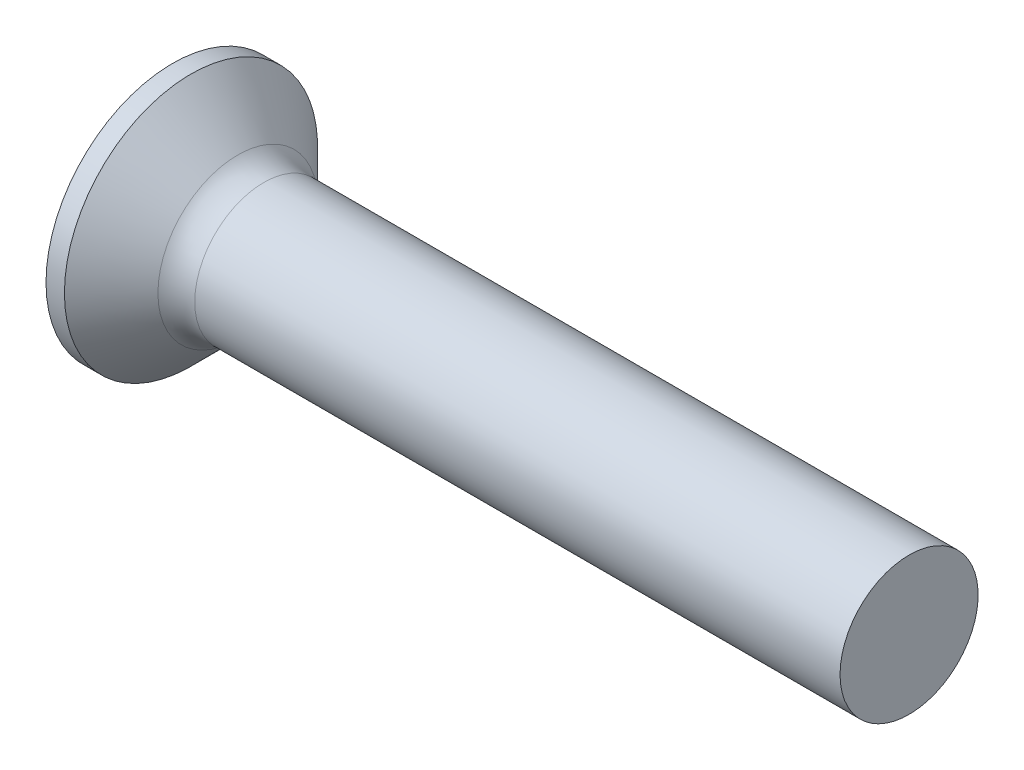
SolidWorks part; units mm, degrees
revolve "Base-Revolve" add sketch "BodySke"
sketch "BodySke" plane through (0, 0, 0) normal (0, 0, 1) x (1, 0, 0)
  line L0 (0, 0) -> (0, 2.75)
  line L1 (0, 2.75) -> (0.4, 2.75)
  line L2 (1.65, 1.5) -> (16, 1.5)
  line L3 (16, 1.5) -> (16, 0)
  line L4 (16, 0) -> (0, 0)
  line L5 (-6.35, 0) -> (82.55, 0) construction
  line L6 (1.65, -1.5) -> (16, -1.5) construction
  line L7 (0.4, -2.75) -> (1.65, -1.5) construction
  line L8 (0.4, 2.75) -> (1.65, 1.5)
  line L9 (0, -2.75) -> (0.4, -2.75) construction
  line L10 (2.15, 3.0875) -> (2.15, -6.4375) construction
  line L11 (0, 6.35) -> (0, -3.175) construction
  dimension "Diameter" = 3
  dimension "Length" = 16
  dimension "Head_ht" = 1.65
  dimension "Head_dia" = 5.5
  dimension "Head_ang" = 90
  dimension "D6" = 0.4
  dimension "Advance" = 0.5
  dimension "Thread_nom" = 16
cosmetic thread "ThreadCosmetic" [suppressed]
fillet "Fillet1" radius 0.8 1 edges at (1.65, 0, 1.5)
ref_plane "Plane1" through (0, 0, 0) normal (0, 0, 1) x (1, 0, 0)
ref_plane "Plane2" through (0, 0, 0) normal (0, 1, 0) x (1, 0, 0)
ref_plane "Plane3" through (0, 0, 0) normal (1, 0, 0) x (0, 0, -1)
sketch "Sketch3" plane through (0, 0, 0) normal (-1, 0, 0) x (0, 0, 1)
  line L0 (-0.37, 1.5) -> (0.37, 1.5)
  line L1 (0.37, 1.5) -> (0.37, -1.5)
  line L2 (0.37, -1.5) -> (-0.37, -1.5)
  line L3 (-0.37, -1.5) -> (-0.37, 1.5)
  dimension "Cross_dia" = 3
  dimension "Cross_width" = 0.74
  dimension "D1" = 1.5
  dimension "D2" = 0.37
ref_plane "Plane4" through (2.01, 0, 0) normal (-1, 0, 0) x (0, 0, 1)
sketch "Sketch4" plane through (2.01, 0, 0) normal (-1, 0, 0) x (0, 0, 1)
  line L0 (-0.37, 0.4979) -> (0.37, 0.4979)
  line L3 (0.37, 0.4979) -> (0.37, -0.4979)
  line L4 (0.37, -0.4979) -> (-0.37, -0.4979)
  line L5 (-0.37, -0.4979) -> (-0.37, 0.4979)
  dimension "D2" = 0.9957
  dimension "D1" = 0.74
  dimension "D4" = 0.4979
  dimension "D3" = 0.37
loft "Recess" cut profiles "Sketch3", "Sketch4"
pattern_circular "RecPat" count 2 every 90 about axis through (0, 0, 0) along (1, 0, 0) of "Recess"
sketch "RecCorSke" plane through (0, 0, 0) normal (0, 0, 1) x (1, 0, 0)
  line L0 (-3.175, 0) -> (15.875, 0) construction
  line L2 (0, 0) -> (0, 0.6966)
  line L3 (0, 0.6966) -> (2.01, 0.556)
  line L4 (2.01, 0.556) -> (2.1907, 0)
  line L5 (2.1907, 0) -> (0, 0)
  dimension "Diameter" = 1.112
  dimension "Depth" = 2.01
  dimension "Draft_angle" = 4
  dimension "Bottom_angle" = 18
revolve "RecessCore" cut sketch "RecCorSke" angle 360 about L0
sketch "ThdSchSke" plane through (0, 0, 0) normal (0, 0, 1) x (1, 0, 0)
  line L0 (2.15, -1.2195) -> (1.9536, -1.5)
  line L1 (2.15, -1.2195) -> (2.3464, -1.5)
  line L2 (2.3464, -1.5) -> (2.3464, -1.875)
  line L3 (-3.175, 0) -> (5.1513, 0) construction
  line L5 (2.3464, -1.875) -> (1.9536, -1.875)
  line L6 (1.9536, -1.875) -> (1.9536, -1.5)
  line L7 (0, 2.75) -> (0, -2.75) construction
  dimension "Diameter" = 3
  dimension "Thread_minor" = 2.439
  dimension "Start" = 2.15
revolve "ThreadSchematic" [suppressed] cut sketch "ThdSchSke" angle 360 about L3
pattern_linear "ThdSchPat" [suppressed]
equation "\"D1@Sketch3\" = \"Cross_dia@Sketch3\" / 2"
equation "\"D2@Sketch3\" = \"Cross_width@Sketch3\" / 2"
equation "\"Depth@RecCorSke\" = \"Cross_depth@Plane4\""
equation "\"D1@Sketch4\" = \"Cross_width@Sketch3\""
equation "\"D2@Sketch4\" = \"Cross_dia@Sketch3\" - 2.0 * \"Cross_depth@Plane4\" * tan(26.5  * 0.017453292)"
equation "\"D3@Sketch4\" = \"D1@Sketch4\" / 2"
equation "\"D4@Sketch4\" = \"D2@Sketch4\" / 2"
equation "\"Thread_length@ThreadCosmetic\" = ((sgn( (\"Length@BodySke\" - \"Advance@BodySke\" * 1.0 - \"Head_ht@BodySke\" ) - \"Thread_nom@BodySke\" )-1)*( (\"Length@BodySke\" - \"Advance@BodySke\" * 1.0 - \"Head_ht@BodySke\" ) - \"Thread_nom@BodySke\" ))/-2+ \"Thread_nom@BodySke\""
equation "\"Thread_minor@ThdSchSke\" = \"Thread_minor@ThreadCosmetic\""
equation "\"Diameter@ThdSchSke\" = \"Diameter@BodySke\""
equation "\"Overcut@ThdSchSke\" = \"Diameter@BodySke\" * 1.25"
equation "\"Start@ThdSchSke\" = 0.000001 + \"Length@BodySke\" - \"Thread_length@ThreadCosmetic\"  '---Countersunk---"
equation "\"Num_threads@ThdSchPat\" = int( \"Thread_length@ThreadCosmetic\" / \"Advance@BodySke\" + 0.999 )  + 1"
equation "\"Advance@ThdSchPat\" = \"Thread_length@ThreadCosmetic\" /  (\"Num_threads@ThdSchPat\" - 1) 'relax it"
